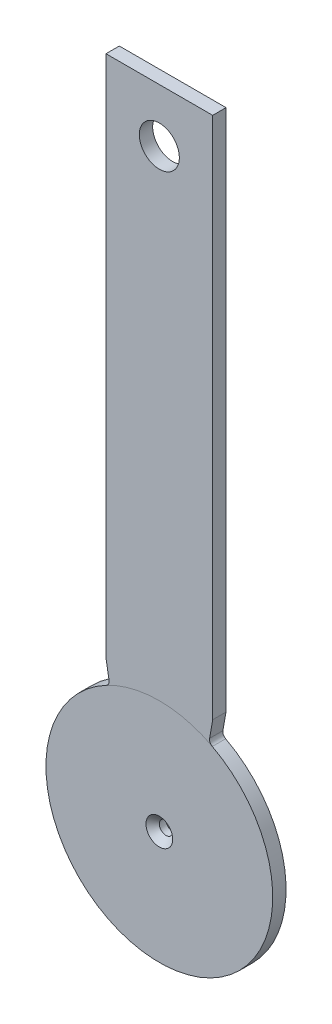
SolidWorks part; units mm, degrees
material "AISI 304"
ref_plane "Front Plane" through (0, 0, 0) normal (0, 0, 1) x (1, 0, 0)
ref_plane "Top Plane" through (0, 0, 0) normal (0, 1, 0) x (1, 0, 0)
ref_plane "Right Plane" through (0, 0, 0) normal (1, 0, 0) x (0, 0, -1)
sketch "Sketch1" plane through (0, 0, 0) normal (0, 0, 1) x (1, 0, 0)
  line L1 (0, -26.9875) -> (0, 153.9875) construction
  line L3 (-12.7, 153.9875) -> (12.7, 153.9875) construction
  circle A0 centre (0, 0) radius 26.9875 construction
  circle A1 centre (0, 0) radius 1.5875 construction
  point P1 (0, 26.9875)
  point P16 (0, 0)
  dimension "OD" = 53.975
  dimension "Orifice Diameter" = 3.175
  dimension "Length" = 180.975
  dimension "Handle Height" = 127
  dimension "Handle Width" = 25.4
sketch "Sketch2" plane through (0, 0, 0) normal (1, 0, 0) x (0, -1, 0)
  line L0 (0, 1.5875) -> (0, -1.5875) construction
  line L1 (-153.9875, -1.5875) -> (26.9875, -1.5875) construction
  line L2 (-153.9875, -1.5875) -> (-153.9875, 1.5875) construction
  line L3 (26.9875, 0) -> (-153.9875, 0) construction
  point P4 (0, 0)
  dimension "Thickness" = 3.175
sketch "Sketch3" plane through (0, 0, 0) normal (0, 0, 1) x (1, 0, 0)
  line L0 (-12.7, 29.4133) -> (-11.9573, 25.2012)
  line L1 (-11.938, 29.4133) -> (-11.938, 23.858) construction
  line L8 (-12.7, 29.4133) -> (-12.7, 153.9875)
  line L9 (-12.7, 153.9875) -> (12.7, 153.9875)
  line L10 (12.7, 153.9875) -> (12.7, 29.4133)
  line L11 (0, -26.9875) -> (0, 153.9875) construction
  line L12 (12.7, 29.4133) -> (11.9573, 25.2012)
  arc A3 (-12.6144, 23.858) -> (12.6144, 23.858) centre (0, 0) ccw
  circle A4 centre (0, 0) radius 1.5875
  circle A5 centre (0, 0) radius 26.9875 construction
  circle A6 centre (0, 0) radius 1.5875 construction
  circle A9 centre (0, 141.2875) radius 4.7625
  arc A10 (-11.9573, 25.2012) -> (-12.6144, 23.858) centre (-13.208, 24.9807) cw
  arc A11 (11.9573, 25.2012) -> (12.6144, 23.858) centre (13.208, 24.9807) ccw
  dimension "D2" = 9.525
  dimension "D5" = 1.27
  dimension "D3" = 12.7
  dimension "D1" = 10
  dimension "D4" = 0.762
  dimension "D6" = 10
extrude "Boss-Extrude1" add sketch "Sketch3" against normal up to vertex (1.5875 mm away) and the other way up to vertex (1.5875 mm away) up to point (0, 0, -1.5875) other way up to point (0, 0, 1.5875)
chamfer "Chamfer1" distance 1.5875 angle 45 1 edges at (1.5875, 0, 1.5875)
sketch "Sketch4" plane through (0, 0, 1.5875) normal (0, 0, 1) x (1, 0, 0)
  circle A0 centre (0, 0) radius 26.9875
  circle A1 centre (0, 0) radius 26.9875 construction
split line "Split Line1"
equation "\"D6@Sketch3\"=\"D1@Sketch3\""
